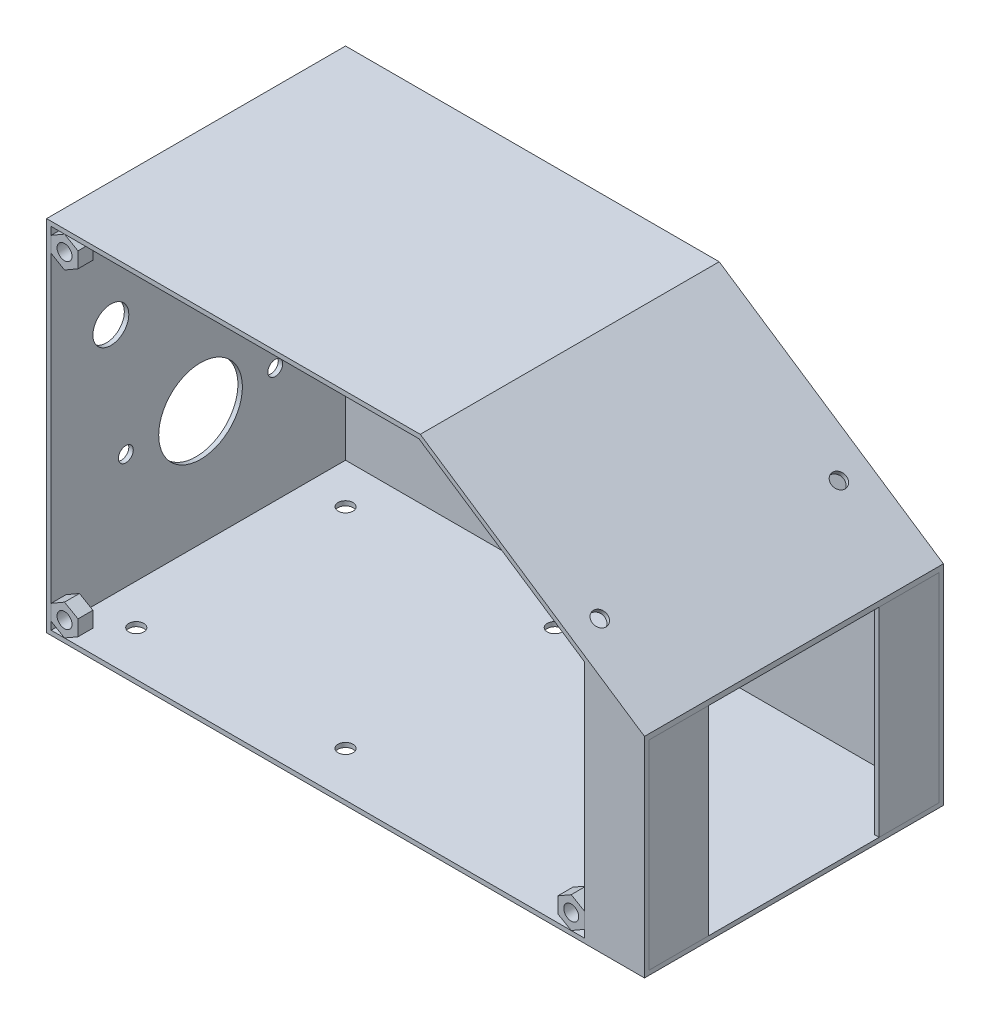
SolidWorks part; units mm, degrees
ref_plane "Front Plane" through (0, 0, 0) normal (0, 0, 1) x (1, 0, 0)
ref_plane "Top Plane" through (0, 0, 0) normal (0, 1, 0) x (1, 0, 0)
ref_plane "Right Plane" through (0, 0, 0) normal (1, 0, 0) x (0, 0, -1)
sketch "Sketch1" plane through (0, 0, 0) normal (0, 0, 1) x (1, 0, 0)
  line L0 (0, 0) -> (0, 120)
  line L1 (0, 120) -> (125, 120)
  line L2 (125, 120) -> (200, 70)
  line L3 (200, 70) -> (200, 0)
  line L4 (200, 0) -> (0, 0)
  dimension "D1" = 120
  dimension "D2" = 200
  dimension "D3" = 70
  dimension "D4" = 125
extrude "Boss-Extrude1" add sketch "Sketch1" along normal blind 100
shell "Shell1" thickness 1.5
sketch "Sketch2" plane through (0, 0, 100) normal (0, 0, 1) x (1, 0, 0)
  line L0 (200, 1.5) -> (200, 68.1972)
  line L1 (200, 68.1972) -> (180, 81.5306)
  line L2 (200, 68.1972) -> (124.5458, 118.5) construction
  line L3 (180, 81.5306) -> (180, 1.5)
  line L4 (1.5, 1.5) -> (200, 1.5) construction
  line L5 (180, 1.5) -> (200, 1.5)
  dimension "D1" = 20
extrude "Boss-Extrude2" add sketch "Sketch2" against normal blind 1.5
sketch "Sketch3" plane through (200, 0, 0) normal (1, 0, 0) x (0, 0, -1)
  line L0 (-50, 70) -> (-50, 0) construction
  line L1 (-100, 70) -> (0, 70) construction
  line L2 (-100, 0) -> (0, 0) construction
  line L3 (-100, 1.5) -> (-1.5, 1.5) construction
  line L4 (-98.5, 68.1972) -> (-78.5, 68.1972)
  line L5 (-98.5, 68.1972) -> (-98.5, 1.5)
  line L6 (-98.5, 1.5) -> (-78.5, 1.5)
  line L7 (-78.5, 68.1972) -> (-78.5, 1.5)
  line L8 (-1.5, 1.5) -> (-21.5, 1.5)
  line L9 (-21.5, 68.1972) -> (-21.5, 1.5)
  line L10 (-1.5, 68.1972) -> (-21.5, 68.1972)
  line L11 (-1.5, 68.1972) -> (-1.5, 1.5)
  line M6 (-1.5, 1.5) -> (-98.5, 1.5)
  line M8 (-98.5, 68.1972) -> (-1.5, 68.1972)
  line M9 (-1.5, 68.1972) -> (-1.5, 1.5)
  dimension "D1" = 20
extrude "Boss-Extrude7" add sketch "Sketch3" against normal blind 1.5 separate body contours L9 M8 M6 M9 | L5 L4 L7 L6
sketch "Sketch4" plane through (0, 0, 0) normal (-1, 0, 0) x (0, 0, 1)
  line L0 (50, 120) -> (50, 0) construction
  line L1 (100, 120) -> (0, 120) construction
  line L2 (100, 0) -> (0, 0) construction
  circle A0 centre (50, 40) radius 14
  circle A1 centre (20, 80) radius 6
  circle A2 centre (80, 80) radius 6
  circle A3 centre (25, 40) radius 2.5
  circle A4 centre (75, 40) radius 2.5
  circle A5 centre (50, 80) radius 6
  dimension "D1" = 28
  dimension "D2" = 12
  dimension "D3" = 60
  dimension "D7" = 5
  dimension "D8" = 40
  dimension "D4" = 40
  dimension "D5" = 40
  dimension "D6" = 25
extrude "Cut-Extrude1" cut sketch "Sketch4" against normal up to next (1.5 mm away)
sketch "Sketch5" plane through (93.8462, 140.7692, 0) normal (0.5547, 0.8321, 0) x (0.8321, -0.5547, 0)
  line L0 (37.4423, -50) -> (127.581, -50) construction
  line L1 (37.4423, -100) -> (37.4423, 0) construction
  line L2 (127.581, -100) -> (127.581, 0) construction
  circle A0 centre (97.581, -10) radius 2.5
  circle A1 centre (97.581, -90) radius 2.5
  dimension "D1" = 80
  dimension "D2" = 30
  dimension "D3" = 5
extrude "Cut-Extrude2" cut sketch "Sketch5" against normal up to next (1.5 mm away)
sketch "Sketch6" plane through (0, 0, 100) normal (0, 0, 1) x (1, 0, 0)
  line L0 (1.5, 118.5) -> (1.5, 1.5) construction
  line L1 (6, 1.5) -> (10.5, 4.0981)
  line L2 (10.5, 4.0981) -> (10.5, 9.2942)
  line L3 (10.5, 9.2942) -> (6, 11.8923)
  line L4 (6, 11.8923) -> (1.5, 9.2942)
  line L5 (1.5, 9.2942) -> (1.5, 4.0981)
  line L6 (1.5, 4.0981) -> (6, 1.5)
  line L7 (1.5, 1.5) -> (180, 1.5) construction
  line L8 (0, 60) -> (200, 60) construction
  line L9 (0, 120) -> (0, 0) construction
  line L10 (200, 0) -> (200, 70) construction
  line L11 (10.5, 115.9019) -> (10.5, 110.7058)
  line L12 (6, 118.5) -> (10.5, 115.9019)
  line L13 (1.5, 115.9019) -> (6, 118.5)
  line L14 (1.5, 110.7058) -> (1.5, 115.9019)
  line L15 (6, 108.1077) -> (1.5, 110.7058)
  line L16 (10.5, 110.7058) -> (6, 108.1077)
  line L17 (90.75, 1.5) -> (90.75, 118.5) construction
  line L18 (124.5458, 118.5) -> (1.5, 118.5) construction
  line L19 (180, 4.0981) -> (175.5, 1.5)
  line L20 (180, 9.2942) -> (180, 4.0981)
  line L21 (175.5, 11.8923) -> (180, 9.2942)
  line L22 (171, 9.2942) -> (175.5, 11.8923)
  line L23 (171, 4.0981) -> (171, 9.2942)
  line L24 (175.5, 1.5) -> (171, 4.0981)
  circle A0 centre (6, 6.6962) radius 4.5 construction
  circle A1 centre (6, 6.6962) radius 2.5
  circle A2 centre (6, 113.3038) radius 2.5
  circle A3 centre (175.5, 6.6962) radius 2.5
  dimension "D1" = 5
  dimension "D2" = 6
extrude "Boss-Extrude8" add sketch "Sketch6" against normal blind 5 separate body
sketch "Sketch8" plane through (0, 0, 0) normal (0, -1, 0) x (1, 0, 0)
  line L0 (100, 100) -> (100, 0) construction
  line L1 (0, 100) -> (200, 100) construction
  line L2 (0, 0) -> (200, 0) construction
  line L3 (0, 50) -> (100, 50) construction
  line L4 (0, 100) -> (0, 0) construction
  circle A0 centre (15, 85) radius 2.5
  circle A1 centre (85, 85) radius 2.5
  circle A2 centre (15, 15) radius 2.5
  circle A3 centre (85, 15) radius 2.5
  dimension "D1" = 70
  dimension "D2" = 70
  dimension "D3" = 5
  dimension "D4" = 5
  dimension "D5" = 15
extrude "Cut-Extrude3" cut sketch "Sketch8" against normal up to next (1.5 mm away)
